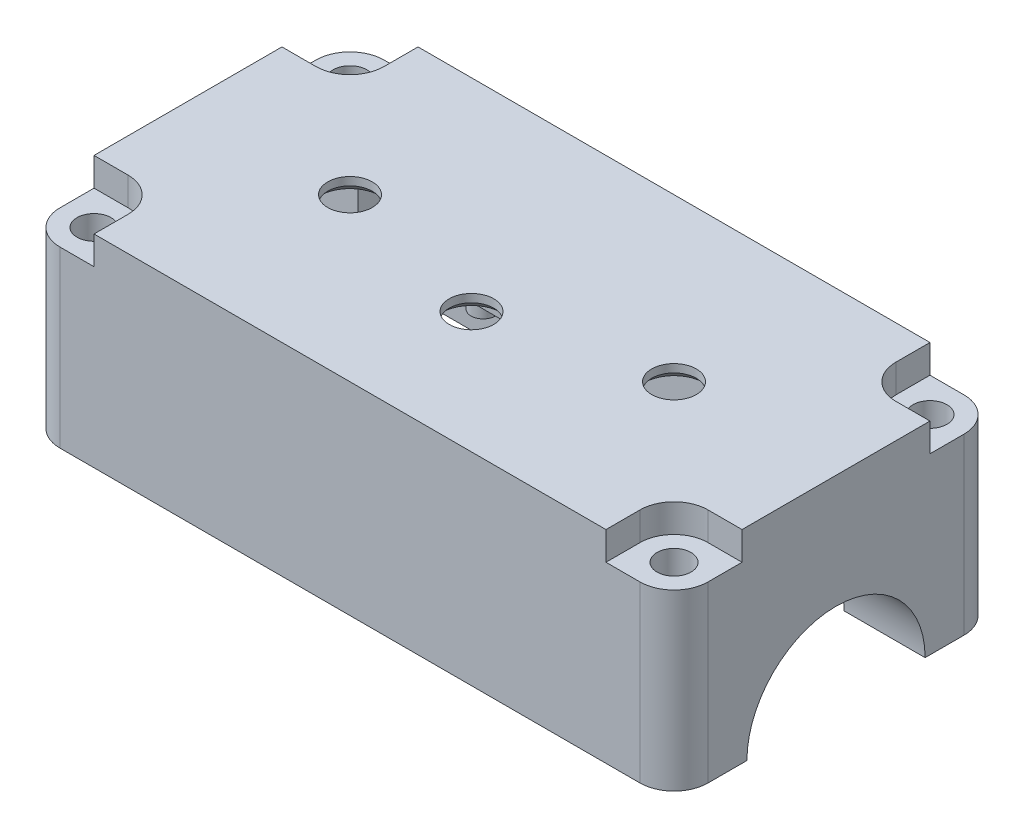
SolidWorks part; units mm, degrees
ref_plane "Front Plane" through (0, 0, 0) normal (0, 0, 1) x (1, 0, 0)
ref_plane "Top Plane" through (0, 0, 0) normal (0, 1, 0) x (1, 0, 0)
ref_plane "Right Plane" through (0, 0, 0) normal (1, 0, 0) x (0, 0, -1)
sketch "Esquisse1" plane through (0, 0, 0) normal (0, 1, 0) x (1, 0, 0)
  line L1 (0, 0) -> (80, 0)
  line L2 (0, 0) -> (0, 40)
  line L3 (0, 40) -> (80, 40)
  line L4 (80, 0) -> (80, 40)
  dimension "D1" = 40
  dimension "D2" = 80
extrude "Boss.-Extru.1" add sketch "Esquisse1" along normal blind 25
sketch "Esquisse5" plane through (0, 0, 0) normal (-1, 0, 0) x (0, 0, 1)
  line L0 (-40, 0) -> (0, 0) construction
  line L1 (-40, 25) -> (0, 25) construction
  line L2 (-38, 23) -> (-2, 23)
  line L3 (-38, 23) -> (-38, 2)
  line L4 (-38, 2) -> (-2, 2)
  line L5 (-2, 23) -> (-2, 2)
  line L6 (-40, 25) -> (-40, 0) construction
  line L7 (0, 25) -> (0, 0) construction
  circle A0 centre (-20, 0) radius 13
  dimension "D1" = 26
  dimension "D2" = 2
  dimension "D3" = 2
  dimension "D4" = 2
  dimension "D5" = 2
extrude "Enlèv. mat.-Extru.4" cut sketch "Esquisse5" against normal blind 78 contours A0 L4 L5 L2 L3
sketch "Esquisse6" plane through (0, 0, -40) normal (0, 0, -1) x (-1, 0, 0)
  line L0 (-80, 0) -> (0, 0) construction
  line L1 (0, 25) -> (-2, 25)
  line L2 (0, 25) -> (0, 0)
  line L3 (0, 0) -> (-2, 0)
  line L4 (-2, 25) -> (-2, 0)
  dimension "D1" = 2
extrude "Boss.-Extru.3" add sketch "Esquisse6" against normal blind 40
sketch "Esquisse7" plane through (0, 0, 0) normal (-1, 0, 0) x (0, 0, 1)
  line L0 (-40, 0) -> (0, 0) construction
  circle A0 centre (-20, 0) radius 11
  dimension "D1" = 22
extrude "Enlèv. mat.-Extru.5" cut sketch "Esquisse7" against normal through all
sketch "Esquisse8" plane through (0, 0, 0) normal (0, -1, 0) x (1, 0, 0)
  line L0 (80, -31) -> (80, -9) construction
  line L1 (70, -38) -> (10, -38)
  line L2 (70, -38) -> (70, -2)
  line L3 (70, -2) -> (10, -2)
  line L4 (10, -38) -> (10, -2)
  line L5 (0, -9) -> (0, -31) construction
  line L6 (80, -40) -> (0, -40) construction
  line L7 (0, 0) -> (80, 0) construction
  dimension "D1" = 10
  dimension "D2" = 10
  dimension "D3" = 2
  dimension "D4" = 2
extrude "Enlèv. mat.-Extru.6" cut sketch "Esquisse8" against normal blind 23
sketch "Esquisse9" plane through (0, 25, 0) normal (0, 1, 0) x (1, 0, 0)
  line L1 (80, 0) -> (70, 0)
  line L2 (80, 0) -> (80, 9)
  line L3 (80, 9) -> (70, 9)
  line L4 (70, 0) -> (70, 9)
  line L5 (0, 0) -> (10, 0)
  line L6 (0, 0) -> (0, 9)
  line L7 (0, 9) -> (10, 9)
  line L8 (10, 0) -> (10, 9)
  line L9 (0, 40) -> (10, 40)
  line L10 (0, 40) -> (0, 31)
  line L11 (0, 31) -> (10, 31)
  line L12 (10, 40) -> (10, 31)
  line L13 (80, 40) -> (70, 40)
  line L14 (80, 40) -> (80, 31)
  line L15 (80, 31) -> (70, 31)
  line L16 (70, 40) -> (70, 31)
  dimension "D1" = 10
  dimension "D2" = 9
  dimension "D3" = 9
  dimension "D4" = 10
  dimension "D5" = 10
  dimension "D6" = 9
  dimension "D7" = 9
  dimension "D8" = 10
extrude "Boss.-Extru.4" add sketch "Esquisse9" against normal blind 23
sketch "Esquisse10" plane through (0, 25, 0) normal (0, 1, 0) x (1, 0, 0)
  line L0 (80, 40) -> (0, 40) construction
  line L1 (80, 0) -> (80, 40) construction
  line L2 (0, 0) -> (80, 0) construction
  line L3 (0, 40) -> (0, 0) construction
  circle A0 centre (75.8, 35.8) radius 2.1
  circle A1 centre (75.8, 4.2) radius 2.1
  circle A2 centre (4.2, 4.2) radius 2.1
  circle A3 centre (4.2, 35.8) radius 2.1
  dimension "D3" = 4.2
  dimension "D4" = 4.2
  dimension "D7" = 4.2
  dimension "D8" = 4.2
  dimension "D1" = 4.2
  dimension "D2" = 4.2
  dimension "D5" = 4.2
  dimension "D6" = 4.2
  dimension "D9" = 4.2
  dimension "D10" = 4.2
  dimension "D11" = 4.2
  dimension "D12" = 4.2
extrude "Enlèv. mat.-Extru.8" cut sketch "Esquisse10" against normal through all
sketch "Esquisse11" plane through (0, 25, 0) normal (0, 1, 0) x (1, 0, 0)
  line L0 (80, 0) -> (80, 40) construction
  line L1 (0, 0) -> (80, 0) construction
  circle A0 centre (60, 20) radius 2.75
  circle A1 centre (40, 15) radius 2.75
  circle A2 centre (20, 20) radius 2.75
  dimension "D1" = 5.5
  dimension "D2" = 5.5
  dimension "D3" = 5.5
  dimension "D4" = 20
  dimension "D5" = 20
  dimension "D6" = 20
  dimension "D7" = 20
  dimension "D8" = 15
  dimension "D9" = 20
extrude "Enlèv. mat.-Extru.9" cut sketch "Esquisse11" against normal through all
chamfer "Chanfrein1" distance 1 angle 45 3 edges at (20, 23, -22.75) (40, 23, -17.75) (60, 23, -22.75)
sketch "Esquisse12" plane through (0, 25, 0) normal (0, 1, 0) x (1, 0, 0)
  line L0 (8.4, 0) -> (8.4, 4.2)
  line L1 (0, 0) -> (80, 0) construction
  line L2 (0, 8.4) -> (4.2, 8.4)
  line L3 (0, 40) -> (0, 0) construction
  line L4 (4.2, 31.6) -> (0, 31.6)
  line L5 (8.4, 35.8) -> (8.4, 40)
  line L6 (80, 40) -> (0, 40) construction
  line L7 (75.8, 31.6) -> (80, 31.6)
  line L8 (80, 0) -> (80, 40) construction
  line L9 (71.6, 35.8) -> (71.6, 40)
  line L10 (71.6, 4.2) -> (71.6, 0)
  line L11 (75.8, 8.4) -> (80, 8.4)
  line L12 (0, 8.4) -> (0, 0)
  line L13 (0, 0) -> (8.4, 0)
  line L14 (0, 31.6) -> (0, 40)
  line L15 (0, 40) -> (8.4, 40)
  line L16 (71.6, 40) -> (80, 40)
  line L17 (80, 40) -> (80, 31.6)
  line L18 (71.6, 0) -> (80, 0)
  line L19 (80, 0) -> (80, 8.4)
  circle A0 centre (4.2, 4.2) radius 4.2
  circle A1 centre (4.2, 35.8) radius 4.2
  circle A2 centre (75.8, 35.8) radius 4.2
  circle A3 centre (75.8, 4.2) radius 4.2
  circle M4 centre (4.2, 35.8) radius 2.1
  circle M5 centre (4.2, 4.2) radius 2.1
  circle M6 centre (75.8, 4.2) radius 2.1
  circle M7 centre (75.8, 35.8) radius 2.1
  line M8 (80, 0) -> (80, 40)
  line M9 (80, 40) -> (0, 40)
  line M10 (0, 40) -> (0, 0)
  line M11 (0, 0) -> (80, 0)
extrude "Enlèv. mat.-Extru.10" cut sketch "Esquisse12" against normal blind 3.5 contours A3 L10 M11 | A3 M6 | A3 L18 M8 | A3 L19 L11 | A2 L7 M8 | A2 M7 | A2 L17 M9 | A2 L16 L9 | A1 L14 L4 | A1 M4 | A1 L15 M10 | A1 L5 M9 | A0 L2 M10 | A0 M5 | A0 L12 M11 | A0 L13 L0
fillet "Congé1" radius 4.2 4 edges at (0, 10.75, 0) (0, 10.75, -40) (80, 10.75, 0) (80, 10.75, -40)
sketch "Esquisse13" plane through (0, 23, 0) normal (0, -1, 0) x (1, 0, 0)
  line L0 (32.45, -24) -> (47.55, -24) construction
  line L1 (32.45, -21) -> (47.55, -21)
  line L2 (32.45, -27) -> (47.55, -27)
  line L5 (70, -38) -> (10, -38) construction
  line L7 (36.5, -27) -> (43.5, -27)
  line L8 (36.5, -27) -> (36.5, -34)
  line L9 (36.5, -34) -> (43.5, -34)
  line L10 (43.5, -27) -> (43.5, -34)
  arc A0 (32.45, -21) -> (32.45, -27) centre (32.45, -24) ccw
  arc A1 (47.55, -27) -> (47.55, -21) centre (47.55, -24) ccw
  point P2 (40, -24)
  dimension "D3" = 14
  dimension "D1" = 3
  dimension "D2" = 15.1
  dimension "D4" = 3.5
  dimension "D5" = 7
  dimension "D6" = 7
extrude "Boss.-Extru.5" add sketch "Esquisse13" along normal blind 3
sketch "Esquisse14" plane through (0, 23, 0) normal (0, -1, 0) x (1, 0, 0)
  line L2 (70, -2) -> (10, -2) construction
  line L3 (70, -9) -> (50, -9)
  line L4 (70, -9) -> (70, -7)
  line L6 (70, -7) -> (50, -7)
  line L8 (50, -9) -> (50, -7)
  line L9 (70, -2) -> (70, -9) construction
  dimension "D1" = 2
  dimension "D2" = 20
  dimension "D3" = 5
  dimension "D4" = 0
extrude "Boss.-Extru.16" add sketch "Esquisse14" along normal blind 5
sketch "Esquisse15" plane through (0, 0, -2) normal (0, 0, -1) x (-1, 0, 0)
  line L0 (-70, 0) -> (-10, 0) construction
  line L1 (-70, 0) -> (-50, 0)
  line L2 (-70, 0) -> (-70, 2)
  line L3 (-70, 2) -> (-50, 2)
  line L4 (-50, 0) -> (-50, 2)
  line L5 (-70, 23) -> (-70, 0) construction
  dimension "D1" = 20
  dimension "D2" = 2
  dimension "D3" = 0
extrude "Boss.-Extru.17" add sketch "Esquisse15" along normal blind 7
sketch "Esquisse17" plane through (0, 0, 0) normal (0, -1, 0) x (1, 0, 0)
  line L0 (50, -9) -> (50, -2) construction
  line L1 (70, -9) -> (50, -9)
  line L2 (70, -9) -> (70, -7)
  line L3 (70, -7) -> (50, -7)
  line L4 (50, -9) -> (50, -7)
  dimension "D1" = 2
extrude "Boss.-Extru.18" add sketch "Esquisse17" against normal blind 11
sketch "Esquisse18" plane through (0, 20, 0) normal (0, -1, 0) x (1, 0, 0)
  circle A0 centre (32.45, -24) radius 1.5
  circle A1 centre (47.55, -24) radius 1.5
  arc A2 (32.45, -21) -> (32.45, -27) centre (32.45, -24) ccw construction
  arc A3 (47.55, -27) -> (47.55, -21) centre (47.55, -24) ccw construction
  point P12 (50.55, -24)
  dimension "D1" = 3
  dimension "D2" = 3
  dimension "D3" = 3
  dimension "D4" = 15.1
extrude "Boss.-Extru.19" add sketch "Esquisse18" along normal blind 3
